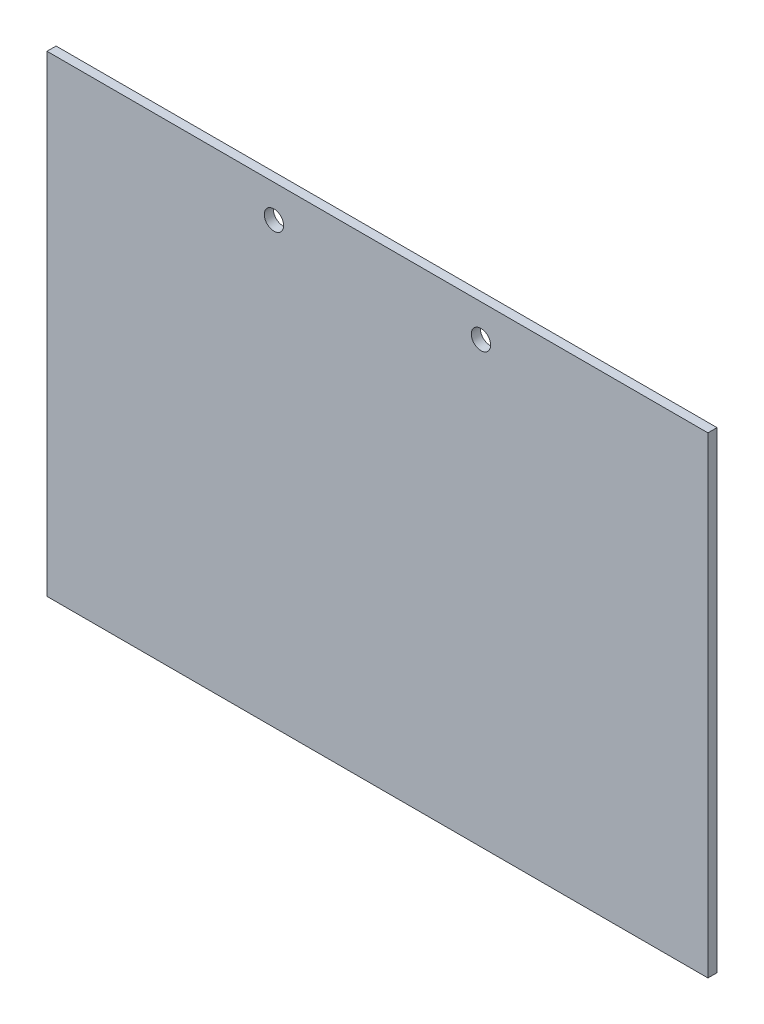
SolidWorks part; units mm, degrees
ref_plane "Front Plane" through (0, 0, 0) normal (0, 0, 1) x (1, 0, 0)
ref_plane "Top Plane" through (0, 0, 0) normal (0, 1, 0) x (1, 0, 0)
ref_plane "Right Plane" through (0, 0, 0) normal (1, 0, 0) x (0, 0, -1)
sketch "Sketch1" plane through (0, 0, 0) normal (0, 0, 1) x (1, 0, 0)
  line L1 (0, 0) -> (231.14, 0)
  line L2 (0, 0) -> (0, -165.1)
  line L3 (0, -165.1) -> (231.14, -165.1)
  line L4 (231.14, 0) -> (231.14, -165.1)
  dimension "D1" = 231.14
  dimension "D2" = 165.1
extrude "Boss-Extrude1" add sketch "Sketch1" along normal blind 3.175
hole_wizard "1/4 Clearance Hole1" positions "Sketch4" profile "Sketch5" hole size "1/4" standard "ANSI Inch" end condition through all
sketch "Sketch4" plane through (0, 0, 3.175) normal (0, 0, 1) x (1, 0, 0)
  line L0 (79.375, -11.43) -> (151.765, -11.43) construction
  line L2 (0, -165.1) -> (231.14, -165.1) construction
  point P0 (79.375, -11.43)
  point P2 (151.765, -11.43)
  point P11 (115.57, -11.43)
  point P12 (115.57, -165.1)
  dimension "D2" = 72.39
  dimension "D3" = 153.67
sketch "Sketch5" plane through (79.375, -11.43, 3.175) normal (1, 0, 0) x (0, -1, 0)
  line L0 (0, 0) -> (0, 3.175)
  line L1 (0, 3.175) -> (3.3782, 3.175)
  line L2 (3.3782, 3.175) -> (3.3782, 0)
  line L5 (3.3782, 0) -> (0, 0)
  line L11 (0, -6.35) -> (0, 107.95) construction
  dimension "Thru Hole Dia." = 6.7564
  dimension "Thru Hole Depth" = 3.175
